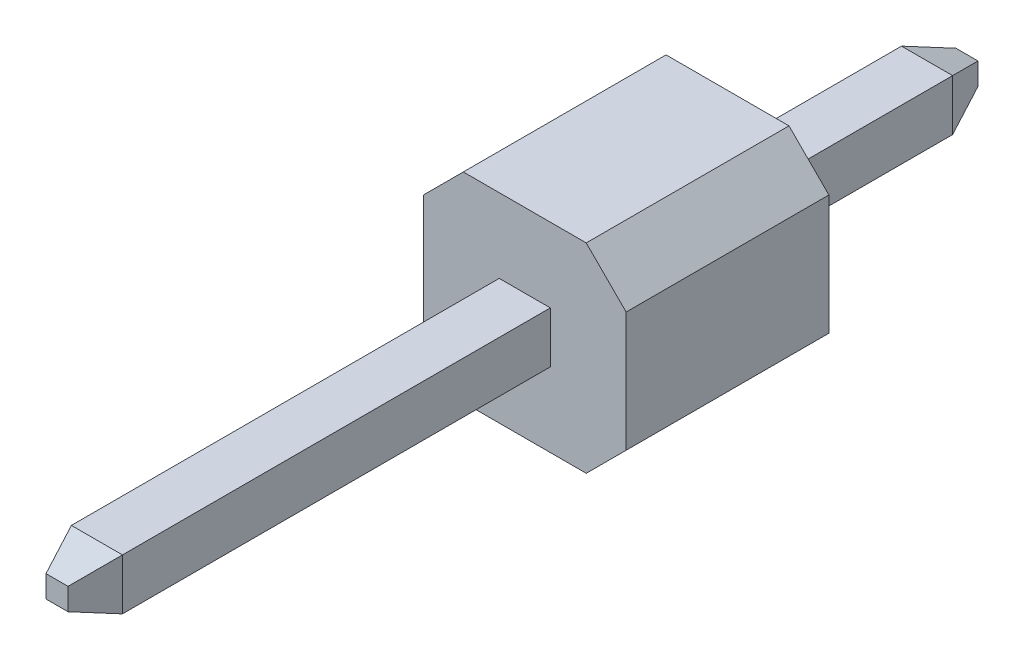
SolidWorks part; units mm, degrees
ref_plane "Front Plane" through (0, 0, 0) normal (0, 0, 1) x (1, 0, 0)
ref_plane "Top Plane" through (0, 0, 0) normal (0, 1, 0) x (1, 0, 0)
ref_plane "Right Plane" through (0, 0, 0) normal (1, 0, 0) x (0, 0, -1)
sketch "Sketch1" plane through (0, 0, 0) normal (0, 0, 1) x (1, 0, 0)
  line L0 (0, 0.32) -> (0, -0.32) construction
  line L1 (-0.32, 0.32) -> (0.32, 0.32)
  line L2 (-0.32, 0.32) -> (-0.32, -0.32)
  line L3 (-0.32, -0.32) -> (0.32, -0.32)
  line L4 (0.32, 0.32) -> (0.32, -0.32)
  point P6 (0, 0)
  dimension "D1" = 0.64
extrude "Boss-Extrude1" add sketch "Sketch1" along normal blind 8.4
sketch "Sketch2" plane through (0, 0, 0) normal (0, 0, -1) x (-1, 0, 0)
  line L1 (0.32, 0.32) -> (-0.32, 0.32)
  line L2 (0.32, 0.32) -> (0.32, -0.32)
  line L3 (0.32, -0.32) -> (-0.32, -0.32)
  line L4 (-0.32, 0.32) -> (-0.32, -0.32)
extrude "Boss-Extrude2" add sketch "Sketch2" along normal blind 3
chamfer "Chamfer1" distance 0.5 angle 20 8 edges at (0.32, 0, 8.4) (0, 0.32, 8.4) (-0.32, 0, 8.4) (0, -0.32, 8.4) (0, 0.32, -3) (-0.32, 0, -3) (0.32, 0, -3) (0, -0.32, -3)
sketch "Sketch3" plane through (0, 0, 0) normal (0, 0, 1) x (1, 0, 0)
  line L0 (0, 1.25) -> (0, -1.25) construction
  line L1 (-1.27, 1.25) -> (1.27, 1.25)
  line L2 (-1.27, 1.25) -> (-1.27, -1.25)
  line L3 (-1.27, -1.25) -> (1.27, -1.25)
  line L4 (1.27, 1.25) -> (1.27, -1.25)
  point P6 (0, 0)
  dimension "D1" = 2.5
  dimension "D2" = 2.54
extrude "Boss-Extrude3" add sketch "Sketch3" along normal blind 2.54
chamfer "Chamfer2" distance 0.5 angle 45 4 edges at (1.27, 1.25, 1.27) (1.27, -1.25, 1.27) (-1.27, 1.25, 1.27) (-1.27, -1.25, 1.27)
sketch "Sketch5" plane through (0, 0, 0) normal (0, 0, -1) x (-1, 0, 0)
  circle A0 centre (0, 0) radius 0.5
